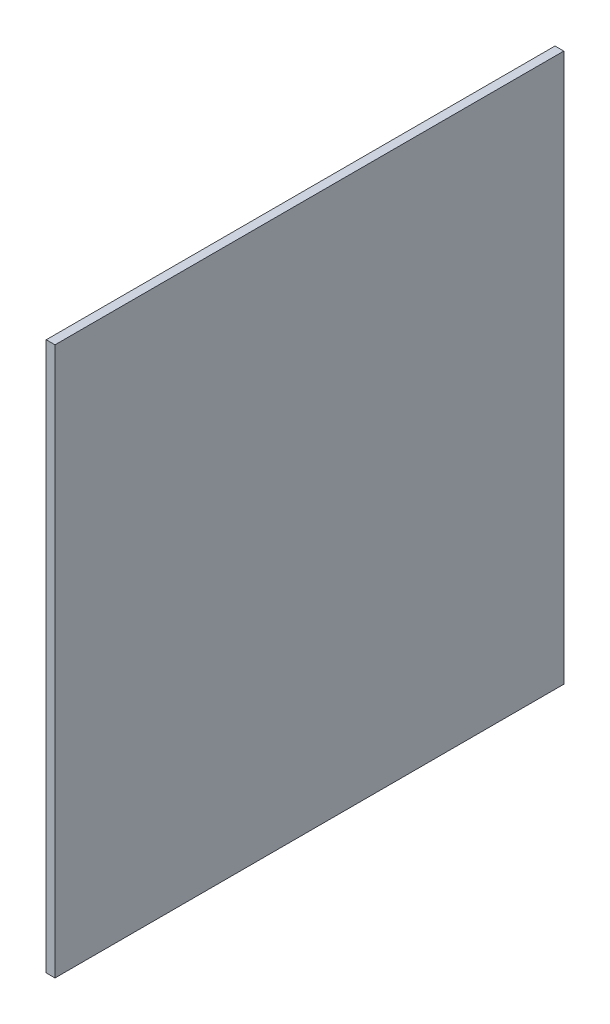
SolidWorks part; units mm, degrees
material "Acrylic (Medium-high impact)"
ref_plane "Front Plane" through (0, 0, 0) normal (0, 0, 1) x (1, 0, 0)
ref_plane "Top Plane" through (0, 0, 0) normal (0, 1, 0) x (1, 0, 0)
ref_plane "Right Plane" through (0, 0, 0) normal (1, 0, 0) x (0, 0, -1)
sketch "Sketch1" plane through (0, 0, 0) normal (1, 0, 0) x (0, 0, -1)
  line L1 (122.4, 2.032) -> (4.572, 2.032)
  line L2 (122.4, 2.032) -> (122.4, 129.032)
  line L3 (122.4, 129.032) -> (4.572, 129.032)
  line L4 (4.572, 2.032) -> (4.572, 129.032)
  dimension "D1" = 127
  dimension "D2" = 117.828
extrude "Boss-Extrude1" add sketch "Sketch1" along normal blind 2.032
